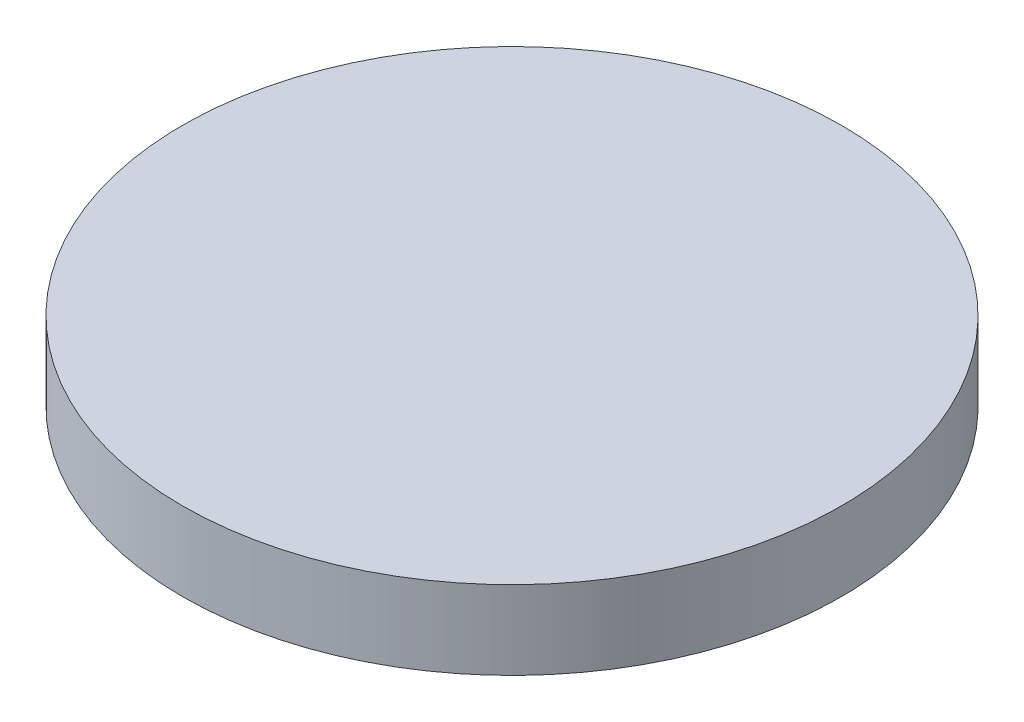
SolidWorks part; units mm, degrees
material "Glass"
ref_plane "Front Plane" through (0, 0, 0) normal (0, 0, 1) x (1, 0, 0)
ref_plane "Top Plane" through (0, 0, 0) normal (0, 1, 0) x (1, 0, 0)
ref_plane "Right Plane" through (0, 0, 0) normal (1, 0, 0) x (0, 0, -1)
sketch "Sketch1" plane through (0, 0, 0) normal (0, 1, 0) x (1, 0, 0)
  circle A0 centre (0, 0) radius 2.096
  circle A1 centre (0, 0) radius 2.096 construction
extrude "Boss-Extrude1" add sketch "Sketch1" along normal blind 0.5
